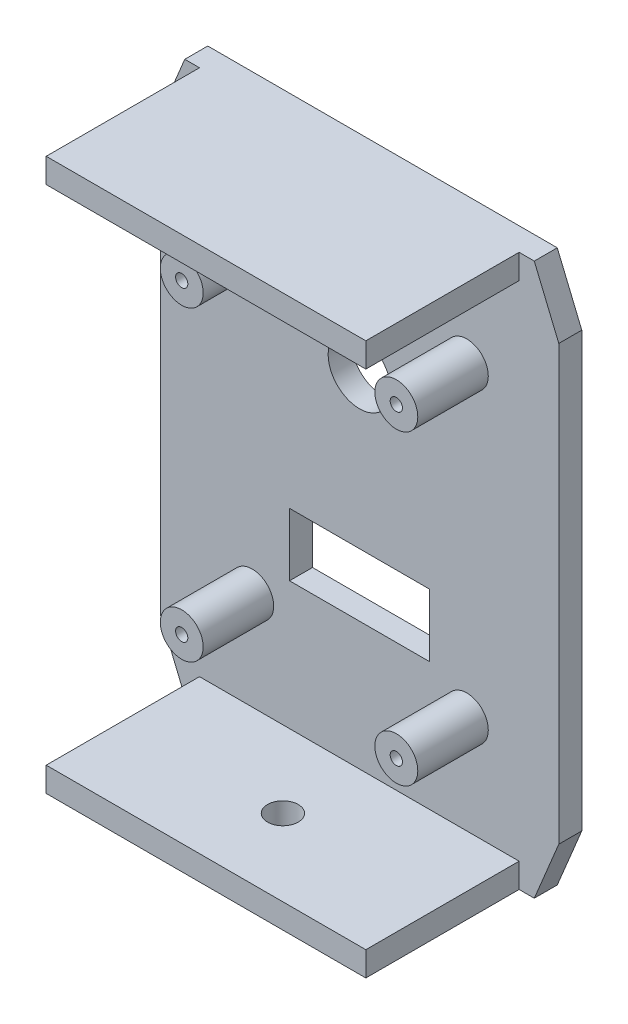
SolidWorks part; units mm, degrees
ref_plane "Front Plane" through (0, 0, 0) normal (0, 0, 1) x (1, 0, 0)
ref_plane "Top Plane" through (0, 0, 0) normal (0, 1, 0) x (1, 0, 0)
ref_plane "Right Plane" through (0, 0, 0) normal (1, 0, 0) x (0, 0, -1)
sketch "Sketch1" plane through (0, 0, 0) normal (0, 0, 1) x (1, 0, 0)
  line L0 (25.1428, 48.3492) -> (30.2228, 36.1136)
  line L1 (-52.3272, 48.3492) -> (30.2228, 48.3492)
  line L2 (-52.3272, 48.3492) -> (-52.3272, -65.9508)
  line L3 (-52.3272, -65.9508) -> (30.2228, -65.9508)
  line L4 (30.2228, 48.3492) -> (30.2228, -65.9508)
  line L5 (-52.3272, 48.3492) -> (30.2228, -65.9508) construction
  line L6 (-52.3272, -65.9508) -> (30.2228, 48.3492) construction
  line L7 (-11.0522, 24.671) -> (-11.0522, -30.9925) construction
  line L8 (-37.0997, -8.8008) -> (9.9758, -8.8008) construction
  line L9 (-47.2472, 48.3492) -> (-52.3272, 36.1136)
  line L10 (25.1428, -65.9508) -> (30.2228, -53.7152)
  line L11 (-47.2472, -65.9508) -> (-52.3272, -53.7152)
  point P0 (-11.0522, -8.8008)
extrude "Boss-Extrude1" add sketch "Sketch1" along normal blind 4.7625 contours L11 L3 L10 L4 L0 L1 L9 L2
sketch "Sketch3" plane through (0, 0, 4.7625) normal (0, 0, 1) x (1, 0, 0)
  line L0 (-44.1992, 43.2694) -> (22.0017, 43.2694)
  line L1 (-44.1992, 43.2694) -> (-44.1992, 48.3492)
  line L2 (-44.1992, 48.3492) -> (22.0017, 48.3492)
  line L3 (22.0017, 43.2694) -> (22.0017, 48.3492)
  line L4 (-47.2472, 48.3492) -> (25.1428, 48.3492) construction
  line L5 (-68.3673, -8.8008) -> (63.7578, -8.8008) construction
  line L6 (22.0017, -60.871) -> (22.0017, -65.9508)
  line L7 (-44.1992, -60.871) -> (22.0017, -60.871)
  line L8 (-44.1992, -60.871) -> (-44.1992, -65.9508)
  line L9 (-44.1992, -65.9508) -> (22.0017, -65.9508)
  dimension "D1" = 3.048
  dimension "D2" = 0
  dimension "D3" = 66.2009
extrude "Boss-Extrude2" add sketch "Sketch3" along normal blind 31.75
sketch "Sketch4" plane through (0, 0, 0) normal (0, 0, -1) x (-1, 0, 0)
  line L0 (11.0522, -17.5806) -> (11.0522, -65.9508) construction
  line L1 (47.2472, -65.9508) -> (-25.1428, -65.9508) construction
  line L2 (-24.5371, -27.8508) -> (43.3344, -27.8508) construction
  line L4 (-3.4478, -21.3508) -> (25.5522, -21.3508)
  line L5 (-3.4478, -21.3508) -> (-3.4478, -34.3508)
  line L6 (-3.4478, -34.3508) -> (25.5522, -34.3508)
  line L7 (25.5522, -21.3508) -> (25.5522, -34.3508)
  line L8 (-3.4478, -21.3508) -> (25.5522, -34.3508) construction
  line L9 (-3.4478, -34.3508) -> (25.5522, -21.3508) construction
  point P6 (11.0522, -27.8508)
  dimension "D1" = 38.1
  dimension "D2" = 28.9999
  dimension "D3" = 13
extrude "Cut-Extrude1" cut sketch "Sketch4" against normal blind 4.7625
sketch "Sketch5" plane through (0, 0, 0) normal (0, 0, -1) x (-1, 0, 0)
  line L0 (47.2472, 48.3492) -> (-25.1428, 48.3492) construction
  circle A0 centre (11.0522, 10.2492) radius 6.5
  dimension "D1" = 13
  dimension "D2" = 38.1
extrude "Cut-Extrude2" cut sketch "Sketch5" against normal blind 4.7625
sketch "Sketch6" plane through (0, -65.9508, 0) normal (0, -1, 0) x (1, 0, 0)
  circle A0 centre (-11.0522, 20.6375) radius 3.175
  dimension "D1" = 6.35
extrude "Cut-Extrude3" cut sketch "Sketch6" against normal blind 7.3025
sketch "Sketch7" plane through (0, 0, 4.7625) normal (0, 0, 1) x (1, 0, 0)
  line L0 (-52.3272, 36.1136) -> (-52.3272, -53.7152) construction
  line L1 (22.0017, -65.9508) -> (25.1428, -65.9508) construction
  line L2 (-47.2472, 48.3492) -> (-44.1992, 48.3492) construction
  circle A0 centre (11.1728, -40.5508) radius 4.445
  circle A1 centre (-33.2772, -40.5508) radius 4.445
  circle A2 centre (11.1728, 22.9492) radius 4.445
  circle A3 centre (-33.2772, 22.9492) radius 4.445
  dimension "D1" = 44.45
  dimension "D2" = 19.05
  dimension "D3" = 0
  dimension "D4" = 0
  dimension "D5" = 25.4
  dimension "D6" = 0
  dimension "D7" = 25.4
  dimension "D8" = 44.45
extrude "Boss-Extrude3" add sketch "Sketch7" along normal blind 14.605
sketch "Sketch8" plane through (0, 0, 19.3675) normal (0, 0, 1) x (1, 0, 0)
  circle A0 centre (-33.2772, 22.9492) radius 1.27
  circle A1 centre (11.1728, 22.9492) radius 1.27
  circle A2 centre (11.1728, -40.5508) radius 1.27
  circle A3 centre (-33.2772, -40.5508) radius 1.27
  dimension "D1" = 2.54
  dimension "D2" = 2.54
  dimension "D3" = 2.54
  dimension "D4" = 2.54
extrude "Cut-Extrude4" cut sketch "Sketch8" against normal blind 50.8
